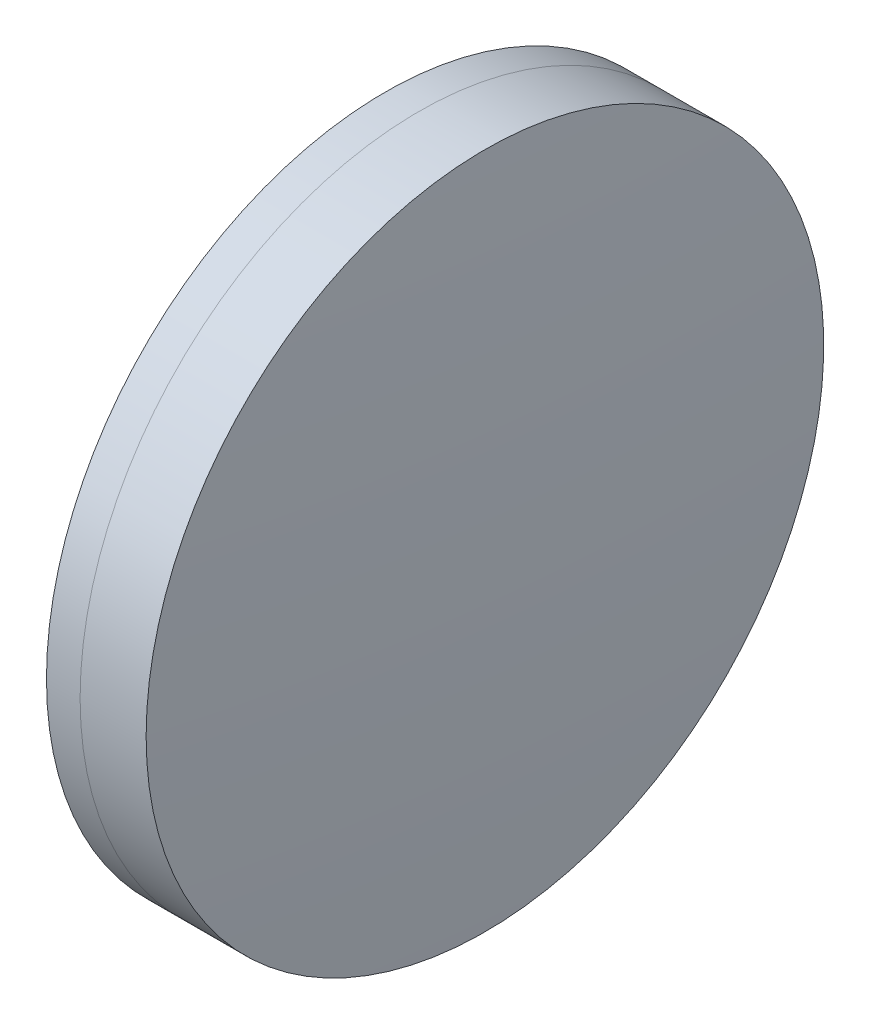
SolidWorks part; units mm, degrees
ref_plane "前视基准面" through (0, 0, 0) normal (0, 0, 1) x (1, 0, 0)
ref_plane "上视基准面" through (0, 0, 0) normal (0, 1, 0) x (1, 0, 0)
ref_plane "右视基准面" through (0, 0, 0) normal (1, 0, 0) x (0, 0, -1)
sketch "草图1" plane through (0, 0, 0) normal (0, 1, 0) x (1, 0, 0)
  line L0 (124.5233, 0) -> (395.1269, 0) construction
  line L1 (259.1361, -15.75) -> (260.6997, -15.75)
  line L2 (259.1361, 15.75) -> (260.6997, 15.75)
  arc A0 (260.6997, -15.75) -> (260.6997, 15.75) centre (180.9032, 0) ccw
  arc A1 (259.1361, 15.75) -> (259.1361, -15.75) centre (381.8182, 0) ccw
  point P10 (258.1292, 0)
  point P11 (262.2392, 0)
  dimension "D3" = 123.689
  dimension "D4" = 81.336
  dimension "D1" = 15.75
  dimension "D2" = 15.75
  dimension "D5" = 4.11
revolve "旋转1" add sketch "草图1" angle 360 about L0
sketch "草图2" plane through (0, 0, 0) normal (0, 1, 0) x (1, 0, 0)
  line L0 (-0.5519, 0) -> (409.4962, 0) construction
  line L2 (260.6997, 15.75) -> (263.769, 15.75)
  line L3 (260.6997, -15.75) -> (263.769, -15.75)
  arc A0 (263.769, -15.75) -> (263.769, 15.75) centre (0.2512, 0) ccw
  arc A1 (260.6997, -15.75) -> (260.6997, 15.75) centre (180.9032, 0) ccw construction
  arc A2 (260.6997, -15.75) -> (260.6997, 15.75) centre (180.9032, 0) ccw
  point P4 (262.2392, 0)
  point P8 (264.2392, 0)
  dimension "D1" = 263.988
  dimension "D2" = 2
revolve "旋转3" add sketch "草图2" angle 360 about L0
